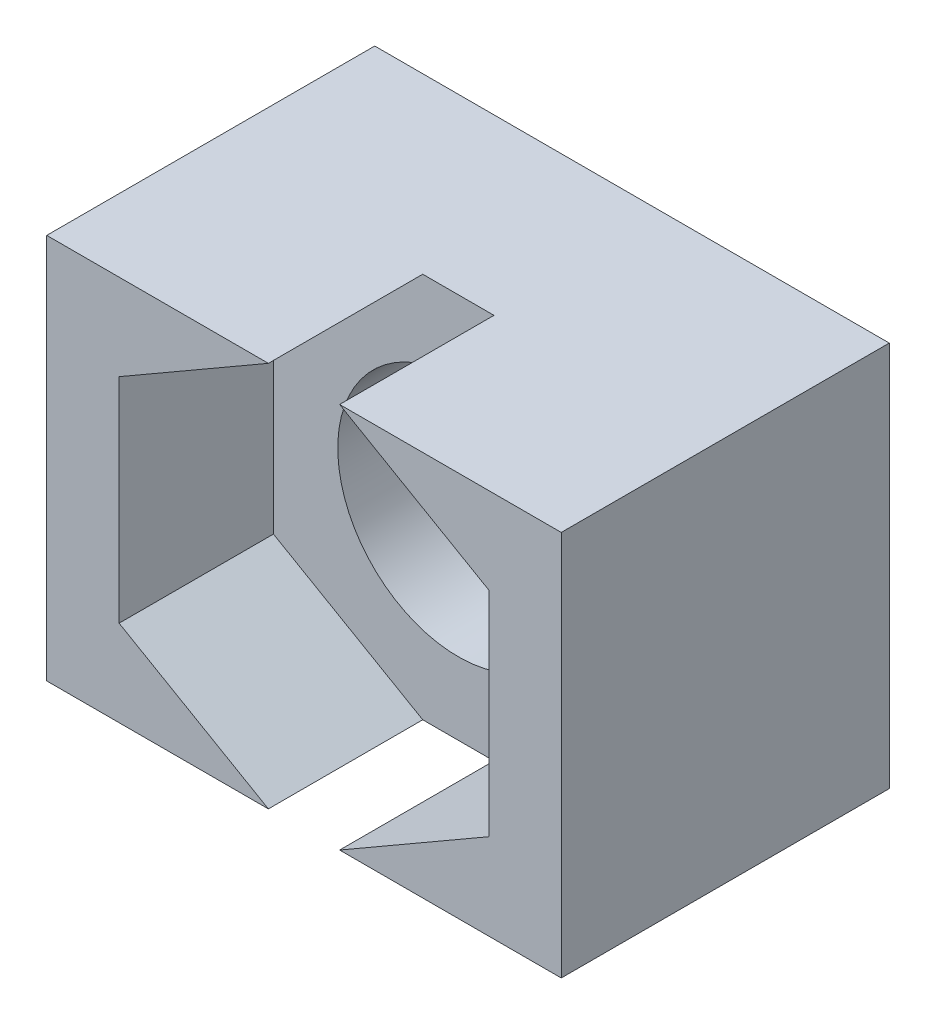
SolidWorks part; units mm, degrees
ref_plane "Plano frontal" through (0, 0, 0) normal (0, 0, 1) x (1, 0, 0)
ref_plane "Plano superior" through (0, 0, 0) normal (0, 1, 0) x (1, 0, 0)
ref_plane "Plano direito" through (0, 0, 0) normal (1, 0, 0) x (0, 0, -1)
sketch "Esboço1" plane through (0, 0, 0) normal (0, 0, 1) x (1, 0, 0)
  line L1 (-4, 3) -> (4, 3)
  line L2 (-4, 3) -> (-4, -3)
  line L3 (-4, -3) -> (4, -3)
  line L4 (4, 3) -> (4, -3)
  line L5 (-4, 3) -> (4, -3) construction
  line L6 (-4, -3) -> (4, 3) construction
  point P0 (0, 0)
  dimension "D1" = 8
  dimension "D2" = 6
extrude "Ressalto-extrusão1" add sketch "Esboço1" along normal blind 5.1
sketch "Esboço2" plane through (0, 0, 5.1) normal (0, 0, 1) x (1, 0, 0)
  line L1 (0, -3.3198) -> (2.875, -1.6599)
  line L2 (2.875, -1.6599) -> (2.875, 1.6599)
  line L3 (2.875, 1.6599) -> (0, 3.3198)
  line L4 (0, 3.3198) -> (-2.875, 1.6599)
  line L5 (-2.875, 1.6599) -> (-2.875, -1.6599)
  line L6 (-2.875, -1.6599) -> (0, -3.3198)
  circle A0 centre (0, 0) radius 2.875 construction
  dimension "D1" = 5.75
extrude "Corte-extrusão1" cut sketch "Esboço2" against normal blind 2.4
sketch "Esboço3" plane through (0, 0, 2.7) normal (0, 0, 1) x (1, 0, 0)
  circle A0 centre (0, 0) radius 1.875
  dimension "D1" = 3.75
extrude "Corte-extrusão2" cut sketch "Esboço3" against normal up to surface (2.7 mm away) up to face at (0, 0, 0)
